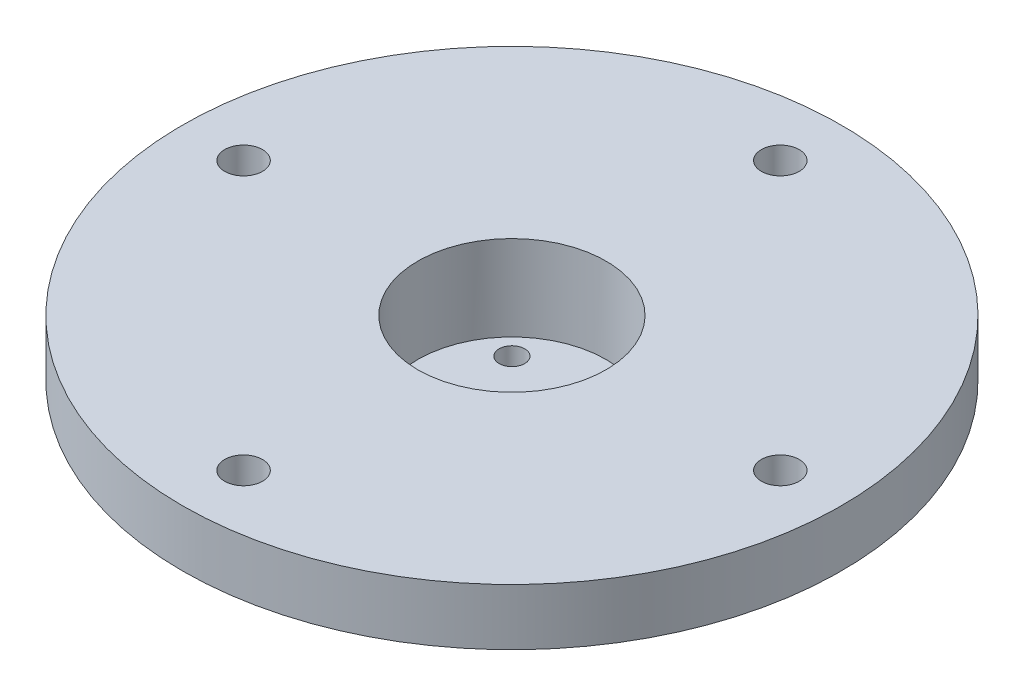
SolidWorks part; units mm, degrees
ref_plane "Front Plane" through (0, 0, 0) normal (0, 0, 1) x (1, 0, 0)
ref_plane "Top Plane" through (0, 0, 0) normal (0, 1, 0) x (1, 0, 0)
ref_plane "Right Plane" through (0, 0, 0) normal (1, 0, 0) x (0, 0, -1)
sketch "Sketch1" plane through (0, 0, 0) normal (0, 1, 0) x (1, 0, 0)
  circle A0 centre (0, 0) radius 15.875
  dimension "D1" = 31.75
extrude "Boss-Extrude1" add sketch "Sketch1" along normal blind 25.4
sketch "Sketch2" plane through (0, 25.4, 0) normal (0, 1, 0) x (1, 0, 0)
  circle A0 centre (0, 0) radius 12.7
  dimension "D1" = 25.4
sketch "Sketch3" plane through (0, 0, 0) normal (0, -1, 0) x (1, 0, 0)
  circle A0 centre (0, 0) radius 9.525
  arc A3 (9.525, 0) -> (6.7352, -6.7352) centre (0, 0) cw
  circle A4 centre (6.7352, -6.7352) radius 1.7272
  circle A5 centre (-6.7352, -6.7352) radius 1.7272
  circle A6 centre (-6.7352, 6.7352) radius 1.7272
  circle A7 centre (6.7352, 6.7352) radius 1.7272
  point P15 (0, 0)
  dimension "D1" = 19.05
  dimension "D2" = 4
  dimension "D3" = 3.4544
sketch "Sketch4" plane through (0, 25.4, 0) normal (0, 1, 0) x (1, 0, 0)
  circle A0 centre (0, 0) radius 44.45
  dimension "D1" = 88.9
extrude "Boss-Extrude2" add sketch "Sketch4" against normal blind 7.62
ref_plane "Plane1" through (0, 13.904, 0) normal (0, -1, 0) x (-1, 0, 0)
sketch "Sketch6" plane through (0, 25.4, 0) normal (0, 1, 0) x (1, 0, 0)
  circle A0 centre (0, 0) radius 36.195
  circle A1 centre (0, 36.195) radius 2.5527
  dimension "D1" = 72.39
  dimension "D2" = 5.1054
extrude "Cut-Extrude4" cut sketch "Sketch6" against normal through all contours A1
pattern_circular "CirPattern2" count 4 over 360 about axis through (0, 0, 0) along (0, 1, 0) of "Cut-Extrude4"
extrude "Cut-Extrude5" cut sketch "Sketch2" against normal up to surface (11.496 mm away) contours A0
chamfer "Chamfer1" distance 2.38 angle 45 1 edges at (0, 17.78, 15.875)
extrude "Cut-Extrude6" cut sketch "Sketch3" against normal through all contours A4 | A5 | A6 | A7
